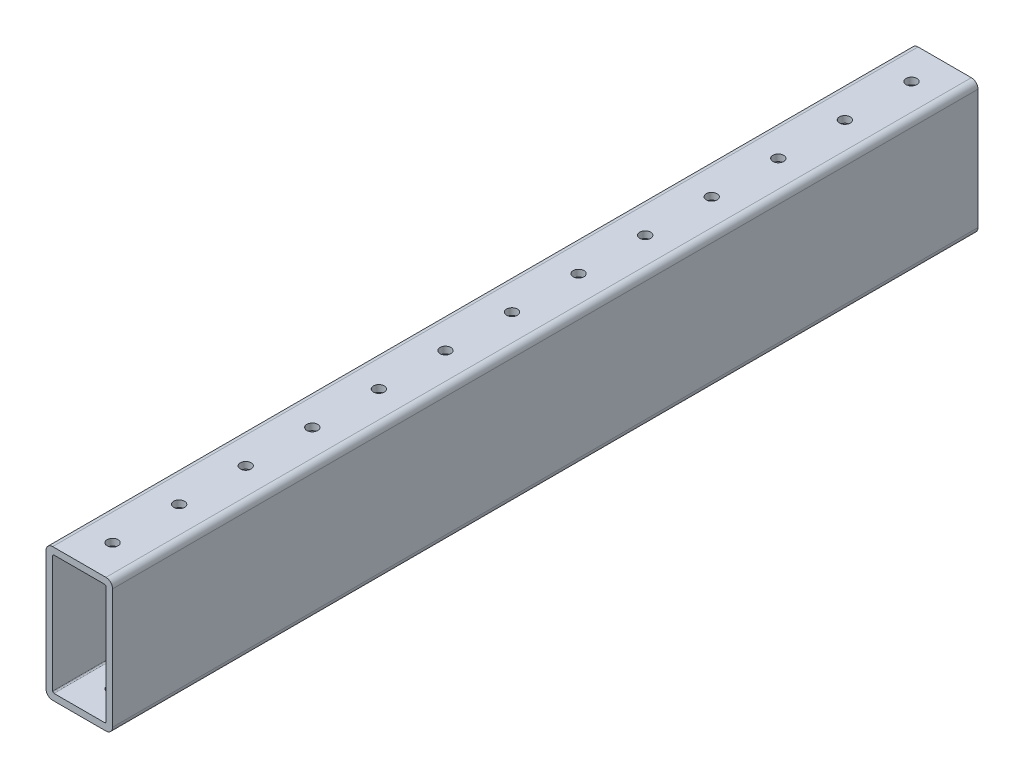
SolidWorks part; units mm, degrees
ref_plane "Front Plane" through (0, 0, 0) normal (0, 0, 1) x (1, 0, 0)
ref_plane "Top Plane" through (0, 0, 0) normal (0, 1, 0) x (1, 0, 0)
ref_plane "Right Plane" through (0, 0, 0) normal (1, 0, 0) x (0, 0, -1)
ref_plane "Plane1" through (12.7, 0, 0) normal (1, 0, 0) x (0, 0, -1)
sketch "Sketch1" plane through (12.7, 0, 0) normal (1, 0, 0) x (0, 0, -1)
  line L0 (165.1, -25.4) -> (165.1, 25.4)
  line L1 (165.1, 25.4) -> (-165.1, 25.4)
  line L2 (-165.1, 25.4) -> (-165.1, -25.4)
  line L3 (-165.1, -25.4) -> (165.1, -25.4)
  point P5 (0, 25.4)
  dimension "D1" = 50.8
  dimension "D2" = 25.4
  dimension "D3" = 330.2
extrude "Boss-Extrude1" add sketch "Sketch1" against normal blind 25.4
sketch "Sketch2" plane through (0, 0, -165.1) normal (0, 0, -1) x (-1, 0, 0)
  line L0 (10.16, -22.86) -> (10.16, 22.86)
  line L1 (10.16, 22.86) -> (-10.16, 22.86)
  line L2 (-10.16, 22.86) -> (-10.16, -22.86)
  line L3 (-10.16, -22.86) -> (10.16, -22.86)
extrude "Cut-Extrude1" cut sketch "Sketch2" against normal through all
hole_wizard "#6 Clearance Hole1" positions "Sketch4" profile "Sketch3" hole size "#6" standard "ANSI Inch"
sketch "Sketch4" plane through (0, -25.4, 0) normal (0, -1, 0) x (-1, 0, 0)
  point P0 (0, 711.2)
  point P1 (0, 736.6)
  point P2 (0, 685.8)
  point P3 (0, 660.4)
  point P4 (0, 635)
  point P5 (0, 609.6)
  point P6 (0, 584.2)
  point P7 (0, 558.8)
  point P8 (0, 533.4)
  point P9 (0, 508)
  point P10 (0, 482.6)
  point P11 (0, 457.2)
  point P12 (0, 431.8)
  point P13 (0, 406.4)
  point P14 (0, 381)
  point P15 (0, 355.6)
  point P16 (0, 330.2)
  point P17 (0, 304.8)
  point P18 (0, 279.4)
  point P19 (0, 254)
  point P20 (0, 228.6)
  point P21 (0, 203.2)
  point P22 (0, 177.8)
  point P23 (0, 152.4)
  point P24 (0, 127)
  point P25 (0, 101.6)
  point P26 (0, 76.2)
  point P27 (0, 50.8)
  point P28 (0, 25.4)
  point P29 (0, 0)
  point P30 (0, -25.4)
  point P31 (0, -50.8)
  point P32 (0, -76.2)
  point P33 (0, -101.6)
  point P34 (0, -127)
  point P35 (0, -152.4)
  point P36 (0, -177.8)
  point P37 (0, -203.2)
  point P38 (0, -228.6)
  point P39 (0, -254)
  point P40 (0, -279.4)
  point P41 (0, -304.8)
  point P42 (0, -330.2)
  point P43 (0, -355.6)
  point P44 (0, -381)
  point P45 (0, -406.4)
  point P46 (0, -431.8)
  point P47 (0, -457.2)
  point P48 (0, -482.6)
  point P49 (0, -508)
  point P50 (0, -533.4)
  point P51 (0, -558.8)
  point P52 (0, -584.2)
  point P53 (0, -609.6)
  point P54 (0, -635)
  point P55 (0, -660.4)
  point P56 (0, -685.8)
  point P57 (0, -711.2)
  point P58 (0, -736.6)
sketch "Sketch3" plane through (0, -25.4, -711.2) normal (1, 0, 0) x (0, 0, -1)
  line L0 (0, 0) -> (0, 50.8)
  line L1 (0, 50.8) -> (2.0701, 50.8)
  line L2 (2.0701, 50.8) -> (2.0701, 0)
  line L5 (2.0701, 0) -> (0, 0)
  line L11 (0, -6.35) -> (0, 107.95) construction
  dimension "Thru Hole Dia." = 4.1402
  dimension "Thru Hole Depth" = 50.8
hole_wizard "#6 Clearance Hole2" positions "Sketch6" profile "Sketch5" hole size "#6" standard "ANSI Inch"
sketch "Sketch6" plane through (0, 25.4, 0) normal (0, 1, 0) x (1, 0, 0)
  point P0 (0, 711.2)
  point P1 (0, 736.6)
  point P2 (0, 685.8)
  point P3 (0, 660.4)
  point P4 (0, 635)
  point P5 (0, 609.6)
  point P6 (0, 584.2)
  point P7 (0, 558.8)
  point P8 (0, 533.4)
  point P9 (0, 508)
  point P10 (0, 482.6)
  point P11 (0, 457.2)
  point P12 (0, 431.8)
  point P13 (0, 406.4)
  point P14 (0, 381)
  point P15 (0, 355.6)
  point P16 (0, 330.2)
  point P17 (0, 304.8)
  point P18 (0, 279.4)
  point P19 (0, 254)
  point P20 (0, 228.6)
  point P21 (0, 203.2)
  point P22 (0, 177.8)
  point P23 (0, 152.4)
  point P24 (0, 127)
  point P25 (0, 101.6)
  point P26 (0, 76.2)
  point P27 (0, 50.8)
  point P28 (0, 25.4)
  point P29 (0, 0)
  point P30 (0, -25.4)
  point P31 (0, -50.8)
  point P32 (0, -76.2)
  point P33 (0, -101.6)
  point P34 (0, -127)
  point P35 (0, -152.4)
  point P36 (0, -177.8)
  point P37 (0, -203.2)
  point P38 (0, -228.6)
  point P39 (0, -254)
  point P40 (0, -279.4)
  point P41 (0, -304.8)
  point P42 (0, -330.2)
  point P43 (0, -355.6)
  point P44 (0, -381)
  point P45 (0, -406.4)
  point P46 (0, -431.8)
  point P47 (0, -457.2)
  point P48 (0, -482.6)
  point P49 (0, -508)
  point P50 (0, -533.4)
  point P51 (0, -558.8)
  point P52 (0, -584.2)
  point P53 (0, -609.6)
  point P54 (0, -635)
  point P55 (0, -660.4)
  point P56 (0, -685.8)
  point P57 (0, -711.2)
  point P58 (0, -736.6)
sketch "Sketch5" plane through (0, 25.4, -711.2) normal (1, 0, 0) x (0, 0, 1)
  line L0 (0, 0) -> (0, 50.8)
  line L1 (0, 50.8) -> (2.0701, 50.8)
  line L2 (2.0701, 50.8) -> (2.0701, 0)
  line L5 (2.0701, 0) -> (0, 0)
  line L11 (0, -6.35) -> (0, 107.95) construction
  dimension "Thru Hole Dia." = 4.1402
  dimension "Thru Hole Depth" = 50.8
fillet "Fillet1" radius 0.5 4 edges at (10.16, 22.86, 0) (-10.16, -22.86, 0) (-10.16, 22.86, 0) (10.16, -22.86, 0)
fillet "Fillet2" radius 2.54 4 edges at (12.7, 25.4, 0) (-12.7, -25.4, 0) (12.7, -25.4, 0) (-12.7, 25.4, 0)
